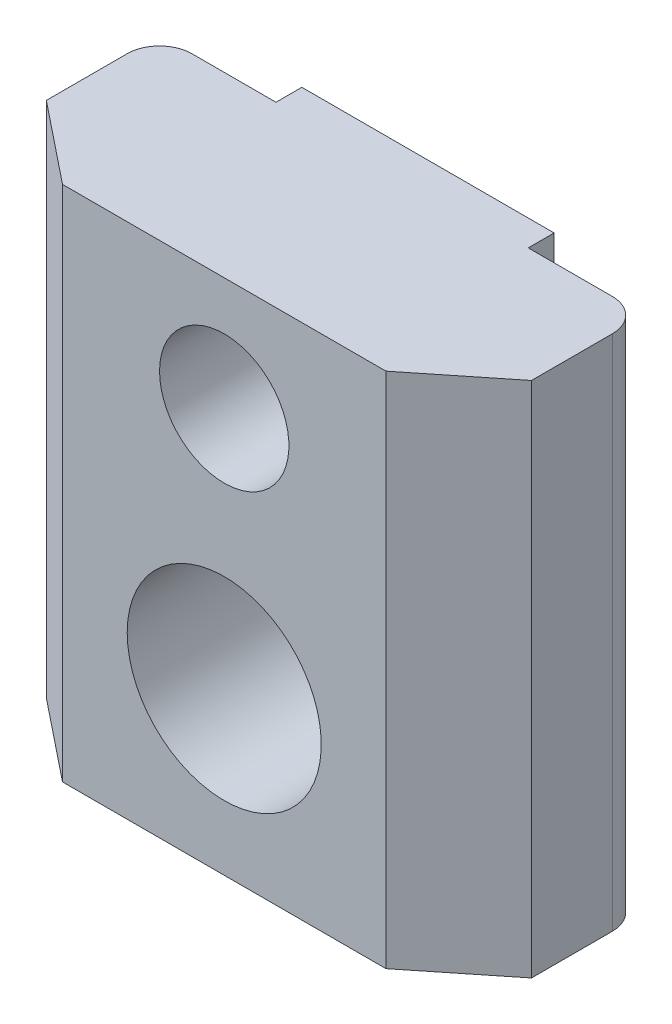
SolidWorks part; units mm, degrees
material "Plain Carbon Steel"
ref_plane "Front Plane" through (0, 0, 0) normal (0, 0, 1) x (1, 0, 0)
ref_plane "Top Plane" through (0, 0, 0) normal (0, 1, 0) x (1, 0, 0)
ref_plane "Right Plane" through (0, 0, 0) normal (1, 0, 0) x (0, 0, -1)
sketch "Sketch1" plane through (0, 0, 0) normal (0, 1, 0) x (1, 0, 0)
  line L0 (0, 0) -> (0, 53.687) construction
  line L1 (0, 0) -> (7.8, 0) construction
  line L2 (-3.9, 0.8) -> (3.9, 0.8)
  line L3 (3.9, 0.8) -> (3.9, 0)
  line L4 (3.9, 0) -> (7.5, 0)
  line L5 (7.5, 0) -> (7.5, -3.5)
  line L6 (7.5, -3.5) -> (5, -5.5)
  line L7 (5, -5.5) -> (-5, -5.5)
  line L8 (-3.9, 0) -> (-7.5, 0)
  line L9 (-7.5, 0) -> (-7.5, -3.5)
  line L10 (-7.5, -3.5) -> (-5, -5.5)
  line L11 (-3.9, 0.8) -> (-3.9, 0)
  dimension "D1" = 6.3
  dimension "D2" = 5.5
  dimension "D3" = 7.8
  dimension "D4" = 15
  dimension "D5" = 10
  dimension "D6" = 2
extrude "Boss-Extrude1" add sketch "Sketch1" along normal blind 11 and the other way blind 5
sketch "Sketch2" plane through (0, 0, -0.8) normal (0, 0, -1) x (-1, 0, 0)
  line L0 (-3.9, 11) -> (3.9, 11) construction
  line L1 (0, 0) -> (0, 7.5) construction
  circle A0 centre (0, 0) radius 3
  circle A1 centre (0, 7.5) radius 2
  point P5 (0, 11)
  dimension "D1" = 6
  dimension "D2" = 4
  dimension "D3" = 3.5
extrude "Cut-Extrude1" cut sketch "Sketch2" against normal through all
fillet "Fillet1" radius 1 2 edges at (7.5, 3, 0) (-7.5, 3, 0)
